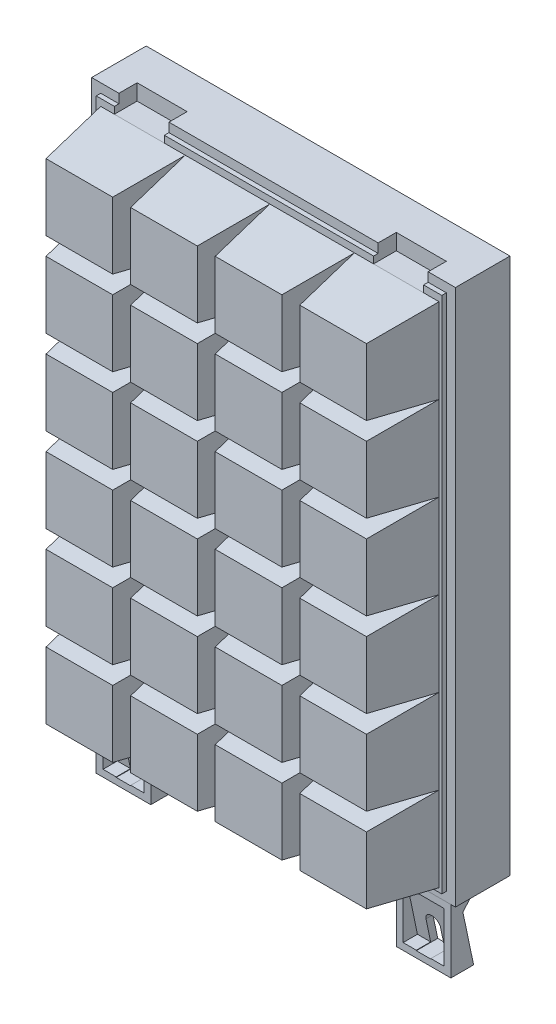
SolidWorks part; units mm, degrees
material "ABS"
ref_plane "TOP" through (0, 0, 0) normal (0, 0, 1) x (1, 0, 0)
ref_plane "FRONT" through (0, 0, 0) normal (0, 1, 0) x (1, 0, 0)
ref_plane "RIGHT" through (0, 0, 0) normal (1, 0, 0) x (0, 0, -1)
sketch "Эскиз1" plane through (0, 0, 0) normal (0, 0, 1) x (1, 0, 0)
  line L0 (-40, 59) -> (40, -59) construction
  line L1 (-40, 59) -> (40, 59)
  line L2 (-40, 59) -> (-40, -59)
  line L3 (-40, -59) -> (40, -59)
  line L4 (40, 59) -> (40, -59)
  point P4 (0, 0)
  dimension "D1" = 118
  dimension "D2" = 80
extrude "Бобышка-Вытянуть1" add sketch "Эскиз1" along normal blind 13
sketch "Эскиз2" plane through (0, 0, 13) normal (0, 0, 1) x (1, 0, 0)
  line L0 (0, 59) -> (0, -59) construction
  line L1 (-37, 55.5) -> (-18.4, 55.5)
  line L2 (-37, 55.5) -> (-37, 36.9)
  line L3 (-37, 36.9) -> (-18.4, 36.9)
  line L4 (-18.4, 55.5) -> (-18.4, 36.9)
  line L5 (-37, 55.5) -> (37, 55.5) construction
  line L6 (-37, 55.5) -> (-37, -55.5) construction
  line L7 (-37, -55.5) -> (37, -55.5) construction
  line L8 (37, 55.5) -> (37, -55.5) construction
  line L9 (40, 59) -> (-40, 59) construction
  line L10 (-40, -59) -> (40, -59) construction
  line L11 (40, 0) -> (-40, 0) construction
  line L12 (40, -59) -> (40, 59) construction
  line L13 (-40, 59) -> (-40, -59) construction
  point P20 (0, 0)
  dimension "D1" = 18.6
  dimension "D2" = 74
  dimension "D3" = 111
extrude "Бобышка-Вытянуть2" add sketch "Эскиз2" along normal blind 14 draft 8
pattern_linear "Линейный массив1" count 4 spacing 18.6 along (1, 0, 0) count 6 spacing 18.6 along (0, -1, 0) of "Бобышка-Вытянуть2"
sketch "Эскиз3" plane through (0, 0, 13) normal (0, 0, 1) x (1, 0, 0)
  line L0 (0, 59) -> (0, 75.7077) construction
  line L1 (40, 59) -> (-40, 59) construction
  line L2 (-18.4, 55.5) -> (-37, 55.5) construction
  line L3 (-34, 59) -> (-23, 59)
  line L4 (-34, 59) -> (-34, 55.5)
  line L5 (-34, 55.5) -> (-23, 55.5)
  line L6 (-23, 59) -> (-23, 55.5)
  line L7 (23, 59) -> (23, 55.5)
  line L8 (34, 55.5) -> (23, 55.5)
  line L9 (34, 59) -> (34, 55.5)
  line L10 (34, 59) -> (23, 59)
  dimension "D1" = 11
  dimension "D2" = 46
extrude "Вырез-Вытянуть1" cut sketch "Эскиз3" against normal blind 5
sketch "Эскиз5" plane through (0, 0, 13) normal (0, 0, 1) x (1, 0, 0)
  line L7 (-40, 59) -> (40, 59)
  line L10 (-40, 59) -> (-40, -59)
  line L11 (-40, -59) -> (40, -59)
  line L12 (40, 59) -> (40, -59)
extrude "Вырез-Вытянуть-Тонкостенный1" cut sketch "Эскиз5" against normal blind 1 thin
sketch "Эскиз4" plane through (0, 0, 12) normal (0, 0, 1) x (1, 0, 0)
  line L0 (-40, -59) -> (40, -59) construction
  line L1 (-39, -59) -> (-27, -59)
  line L2 (-39, -59) -> (-39, -73)
  line L3 (-39, -73) -> (-27, -73)
  line L4 (-27, -59) -> (-27, -73)
  line L5 (0, -59) -> (0, -75.6828) construction
  line L10 (-33, -59) -> (-33, -73) construction
  line L11 (34.3352, -65) -> (31.1352, -65) construction
  line L12 (-34.3352, -65) -> (-31.1352, -65) construction
  line L13 (-34.6, -66.6) -> (-34.6, -71.6)
  line L14 (-34.6, -71.6) -> (-31.4, -71.6)
  line L15 (-31.4, -66.6) -> (-31.4, -71.6)
  line L16 (33, -59) -> (33, -73) construction
  line L17 (31.4, -66.6) -> (31.4, -71.6)
  line L18 (34.6, -71.6) -> (31.4, -71.6)
  line L19 (34.6, -66.6) -> (34.6, -71.6)
  line L20 (27, -59) -> (27, -73)
  line L21 (39, -73) -> (27, -73)
  line L22 (39, -59) -> (39, -73)
  line L23 (39, -59) -> (27, -59)
  arc A0 (-31.4, -66.6) -> (-34.6, -66.6) centre (-33, -66.6) ccw
  arc A1 (31.4, -66.6) -> (34.6, -66.6) centre (33, -66.6) cw
  dimension "D1" = 14
  dimension "D2" = 12
  dimension "D3" = 3.2
  dimension "D4" = 1.4
  dimension "D5" = 8
  dimension "D6" = 54
extrude "Бобышка-Вытянуть3" add sketch "Эскиз4" against normal blind 5 separate body
sketch "Эскиз6" plane through (-39, 0, 0) normal (-1, 0, 0) x (0, 0, 1)
  line L0 (7, -73) -> (9.3502, -61.8006)
  line L1 (9.3502, -61.8006) -> (7, -59)
  line L2 (7, -59) -> (7, -73) construction
  line L3 (7, -59) -> (12, -59) construction
  line L4 (7, -59) -> (7, -73)
  point P10 (9.3502, -61.8006)
extrude "Вырез-Вытянуть2" cut sketch "Эскиз6" against normal through all
sketch "Эскиз7" plane through (0, 0, 12) normal (0, 0, 1) x (1, 0, 0)
  line L0 (-37.5, -60.5) -> (-28.5, -60.5)
  line L1 (-39, -59) -> (-27, -59) construction
  line L2 (-39, -59) -> (-39, -73) construction
  line L3 (-39, -73) -> (-27, -73) construction
  line L4 (-27, -59) -> (-27, -73) construction
  line L5 (27, -59) -> (39, -59) construction
  line L6 (27, -59) -> (27, -73) construction
  line L7 (27, -73) -> (39, -73) construction
  line L8 (39, -59) -> (39, -73) construction
  line L9 (-28.5, -60.5) -> (-28.5, -71.5)
  line L10 (-37.5, -71.5) -> (-28.5, -71.5)
  line L11 (-37.5, -60.5) -> (-37.5, -71.5)
  line L12 (28.5, -60.5) -> (37.5, -60.5)
  line L13 (37.5, -60.5) -> (37.5, -71.5)
  line L14 (28.5, -71.5) -> (37.5, -71.5)
  line L15 (28.5, -60.5) -> (28.5, -71.5)
  dimension "D1" = 1.5
extrude "Вырез-Вытянуть3" cut sketch "Эскиз7" against normal offset from surface (0.8442 mm away) 1.5
equation "\"D3@Линейный массив1\"=\"D1@Эскиз2\""
equation "\"D4@Линейный массив1\"=\"D1@Эскиз2\""
